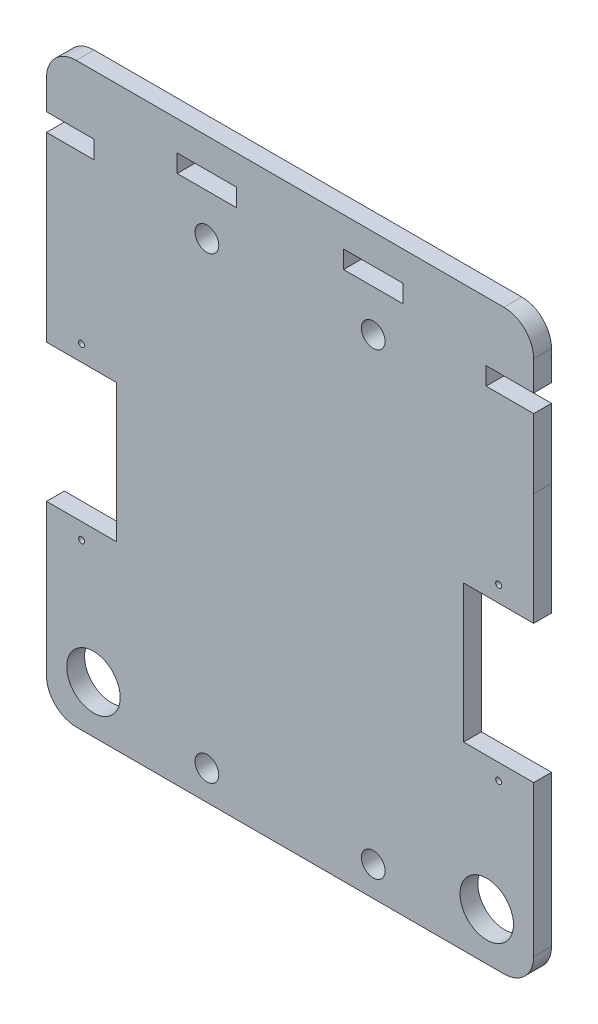
SolidWorks part; units mm, degrees
ref_plane "Alzado" through (0, 0, 0) normal (0, 0, 1) x (1, 0, 0)
ref_plane "Planta" through (0, 0, 0) normal (0, 1, 0) x (1, 0, 0)
ref_plane "Vista lateral" through (0, 0, 0) normal (1, 0, 0) x (0, 0, -1)
sketch "Model" plane through (0, 0, 0) normal (0, 0, 1) x (1, 0, 0)
  line L0 (50.4652, 72.8238) -> (50.4652, 69.8238)
  line L1 (50.4652, 69.8238) -> (60.4652, 69.8238)
  line L2 (60.4652, 69.8238) -> (60.4652, 72.8238)
  line L3 (60.4652, 72.8238) -> (50.4652, 72.8238)
  line L4 (22.4652, 72.8238) -> (22.4652, 69.8238)
  line L5 (22.4652, 69.8238) -> (32.4652, 69.8238)
  line L6 (32.4652, 69.8238) -> (32.4652, 72.8238)
  line L7 (32.4652, 72.8238) -> (22.4652, 72.8238)
  line L8 (0.4683, 11.04) -> (0.4683, -14.36)
  line L9 (5.4683, -19.36) -> (77.4652, -19.36)
  line L10 (82.4652, -14.36) -> (82.4652, -9.055)
  line L11 (82.4652, -9.055) -> (82.4652, 11.04)
  line L12 (82.4652, 11.04) -> (70.6652, 11.04)
  line L13 (70.6652, 11.04) -> (70.6652, 34.24)
  line L14 (70.6652, 34.24) -> (82.4652, 34.24)
  line L15 (82.4652, 34.24) -> (82.4652, 53.1454)
  line L16 (82.4652, 53.1454) -> (82.4621, 64.8238)
  line L17 (82.4621, 64.8238) -> (74.4621, 64.8238)
  line L18 (74.4621, 64.8238) -> (74.4621, 67.8238)
  line L19 (74.4621, 67.8238) -> (82.4621, 67.8238)
  line L20 (82.4621, 67.8238) -> (82.4652, 72.8238)
  line L21 (77.4652, 77.8238) -> (67.9482, 77.8238)
  line L22 (67.9482, 77.8238) -> (45.2057, 77.8238)
  line L23 (45.2057, 77.8238) -> (23.0936, 77.8238)
  line L24 (23.0936, 77.8238) -> (11.9421, 77.8238)
  line L25 (11.9421, 77.8238) -> (5.4683, 77.8238)
  line L26 (0.4683, 72.8238) -> (0.4683, 67.8238)
  line L27 (0.4683, 67.8238) -> (8.4683, 67.8238)
  line L28 (8.4683, 67.8238) -> (8.4683, 64.8238)
  line L29 (8.4683, 64.8238) -> (0.4683, 64.8238)
  line L30 (0.4683, 64.8238) -> (0.4683, 34.24)
  line L31 (0.4683, 34.24) -> (12.2683, 34.24)
  line L32 (12.2683, 34.24) -> (12.2683, 11.04)
  line L33 (12.2683, 11.04) -> (0.4683, 11.04)
  circle A0 centre (55.4652, 62.8238) radius 2
  circle A1 centre (27.4652, 62.8238) radius 2
  circle A2 centre (55.4652, -14.36) radius 2
  circle A3 centre (27.4652, -14.36) radius 2
  circle A4 centre (74.5652, -11.36) radius 4.5
  circle A5 centre (8.3652, -11.36) radius 4.5
  circle A6 centre (6.3652, 8.34) radius 0.5
  circle A7 centre (6.3652, 36.94) radius 0.5
  circle A8 centre (76.5652, 8.34) radius 0.5
  circle A9 centre (76.5652, 36.94) radius 0.5
  arc A10 (0.4683, -14.36) -> (5.4683, -19.36) centre (5.4683, -14.36) ccw
  arc A11 (77.4652, -19.36) -> (82.4652, -14.36) centre (77.4652, -14.36) ccw
  arc A12 (82.4652, 72.8238) -> (77.4652, 77.8238) centre (77.4652, 72.8238) ccw
  arc A13 (5.4683, 77.8238) -> (0.4683, 72.8238) centre (5.4683, 72.8238) ccw
extrude "Saliente-Extruir1" add sketch "Model" along normal blind 3
